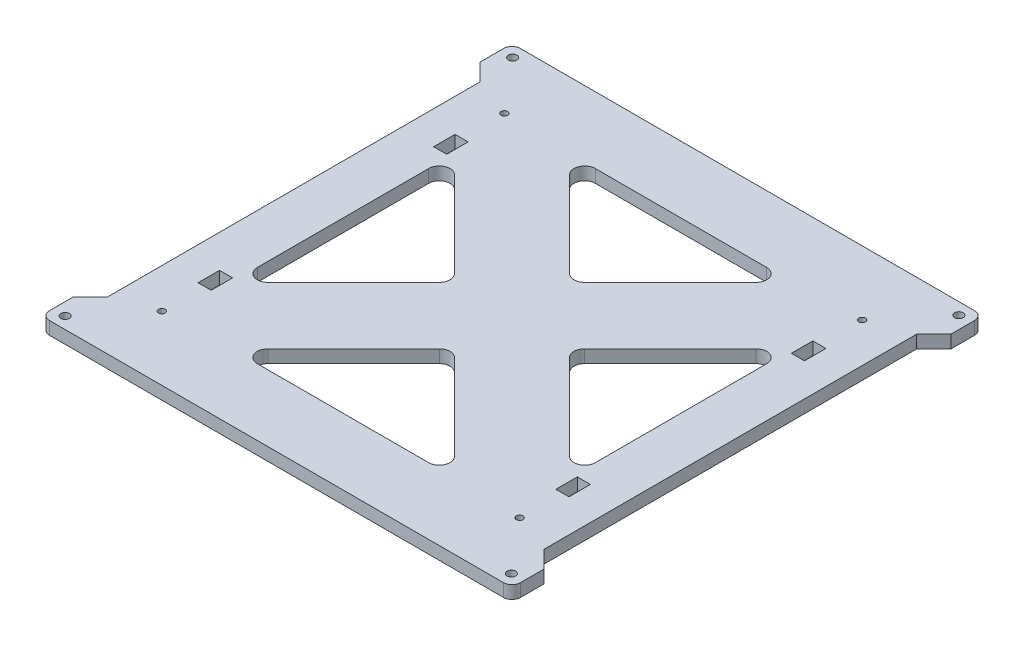
SolidWorks part; units mm, degrees
ref_plane "Спереди" through (0, 0, 0) normal (0, 0, 1) x (1, 0, 0)
ref_plane "Сверху" through (0, 0, 0) normal (0, 1, 0) x (1, 0, 0)
ref_plane "Справа" through (0, 0, 0) normal (1, 0, 0) x (0, 0, -1)
sketch "Эскиз1" plane through (0, 0, 0) normal (0, 1, 0) x (1, 0, 0)
  line L0 (-105.8411, 66.194) -> (-105.8411, 56.194)
  line L1 (-105.8411, 56.194) -> (-99.7411, 56.194)
  line L2 (-99.7411, 56.194) -> (-99.7411, 66.194)
  line L3 (-99.7411, 66.194) -> (-105.8411, 66.194)
  line L4 (67.3589, -53.806) -> (67.3589, -43.806)
  line L5 (67.3589, -43.806) -> (61.2589, -43.806)
  line L6 (61.2589, -43.806) -> (61.2589, -53.806)
  line L7 (61.2589, -53.806) -> (67.3589, -53.806)
  line L8 (-59.2411, -72.7471) -> (20.7589, -72.7471)
  line L9 (24.2945, -64.2115) -> (-15.7055, -24.2115)
  line L10 (-22.7766, -24.2115) -> (-62.7766, -64.2115)
  line L11 (61.2589, 56.194) -> (67.3589, 56.194)
  line L12 (67.3589, 56.194) -> (67.3589, 66.194)
  line L13 (67.3589, 66.194) -> (61.2589, 66.194)
  line L14 (61.2589, 66.194) -> (61.2589, 56.194)
  line L15 (-121.2411, -80.806) -> (-129.2411, -88.806)
  line L16 (-121.2411, 93.194) -> (-121.2411, -80.806)
  line L17 (-129.2411, 101.194) -> (-121.2411, 93.194)
  line L18 (-129.2411, 112.194) -> (-129.2411, 101.194)
  line L19 (86.7589, 116.194) -> (-125.2411, 116.194)
  line L20 (90.7589, 101.194) -> (90.7589, 112.194)
  line L21 (82.7589, 93.194) -> (90.7589, 101.194)
  line L22 (82.7589, -80.806) -> (82.7589, 93.194)
  line L23 (90.7589, -88.806) -> (82.7589, -80.806)
  line L24 (90.7589, -99.806) -> (90.7589, -88.806)
  line L25 (-125.2411, -103.806) -> (86.7589, -103.806)
  line L26 (-129.2411, -88.806) -> (-129.2411, -99.806)
  line L27 (20.7589, 85.1352) -> (-59.2411, 85.1352)
  line L28 (-62.7766, 76.5996) -> (-22.7766, 36.5996)
  line L29 (-15.7055, 36.5996) -> (24.2945, 76.5996)
  line L30 (59.7, -33.806) -> (59.7, 46.194)
  line L31 (51.1645, 49.7296) -> (11.1645, 9.7296)
  line L32 (11.1645, 2.6585) -> (51.1645, -37.3415)
  line L33 (-98.1822, 46.194) -> (-98.1822, -33.806)
  line L34 (-89.6467, -37.3415) -> (-49.6467, 2.6585)
  line L35 (-49.6467, 9.7296) -> (-89.6467, 49.7296)
  line L36 (-99.7411, -43.806) -> (-105.8411, -43.806)
  line L37 (-105.8411, -43.806) -> (-105.8411, -53.806)
  line L38 (-105.8411, -53.806) -> (-99.7411, -53.806)
  line L39 (-99.7411, -53.806) -> (-99.7411, -43.806)
  circle A0 centre (-123.4411, -98.306) radius 2
  circle A1 centre (84.9589, -98.306) radius 2
  circle A2 centre (-123.4411, 110.694) radius 2
  circle A3 centre (84.9589, 110.694) radius 2
  arc A4 (20.7589, -72.7471) -> (24.2945, -64.2115) centre (20.7589, -67.7471) ccw
  arc A5 (-15.7055, -24.2115) -> (-22.7766, -24.2115) centre (-19.2411, -27.7471) ccw
  arc A6 (-62.7766, -64.2115) -> (-59.2411, -72.7471) centre (-59.2411, -67.7471) ccw
  arc A7 (-125.2411, 116.194) -> (-129.2411, 112.194) centre (-125.2411, 112.194) ccw
  arc A8 (90.7589, 112.194) -> (86.7589, 116.194) centre (86.7589, 112.194) ccw
  arc A9 (86.7589, -103.806) -> (90.7589, -99.806) centre (86.7589, -99.806) ccw
  arc A10 (-129.2411, -99.806) -> (-125.2411, -103.806) centre (-125.2411, -99.806) ccw
  arc A11 (-59.2411, 85.1352) -> (-62.7766, 76.5996) centre (-59.2411, 80.1352) ccw
  arc A12 (-22.7766, 36.5996) -> (-15.7055, 36.5996) centre (-19.2411, 40.1352) ccw
  arc A13 (24.2945, 76.5996) -> (20.7589, 85.1352) centre (20.7589, 80.1352) ccw
  arc A14 (59.7, 46.194) -> (51.1645, 49.7296) centre (54.7, 46.194) ccw
  arc A15 (11.1645, 9.7296) -> (11.1645, 2.6585) centre (14.7, 6.194) ccw
  arc A16 (51.1645, -37.3415) -> (59.7, -33.806) centre (54.7, -33.806) ccw
  arc A17 (-98.1822, -33.806) -> (-89.6467, -37.3415) centre (-93.1822, -33.806) ccw
  arc A18 (-49.6467, 2.6585) -> (-49.6467, 9.7296) centre (-53.1822, 6.194) ccw
  arc A19 (-89.6467, 49.7296) -> (-98.1822, 46.194) centre (-93.1822, 46.194) ccw
  circle A20 centre (64.3089, 86.194) radius 1.55
  circle A21 centre (64.3089, -73.806) radius 1.55
  circle A22 centre (-102.7911, -73.806) radius 1.55
  circle A23 centre (-102.7911, 86.194) radius 1.55
extrude "Бобышка-Вытянуть1" add sketch "Эскиз1" along normal blind 6
